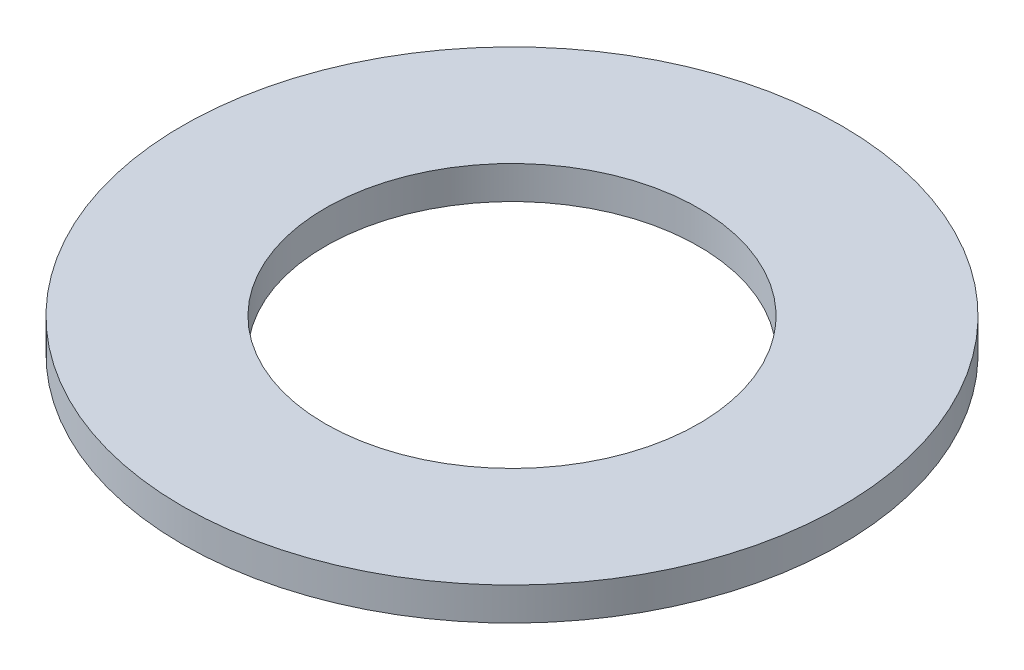
SolidWorks part; units mm, degrees
ref_plane "Front Plane" through (0, 0, 0) normal (0, 0, 1) x (1, 0, 0)
ref_plane "Top Plane" through (0, 0, 0) normal (0, 1, 0) x (1, 0, 0)
ref_plane "Right Plane" through (0, 0, 0) normal (1, 0, 0) x (0, 0, -1)
sketch "Sketch1" plane through (0, 0, 0) normal (0, 1, 0) x (1, 0, 0)
  circle A0 centre (0, 0) radius 17
  circle A1 centre (0, 0) radius 30
extrude "Boss-Extrude1" add sketch "Sketch1" along normal blind 3
